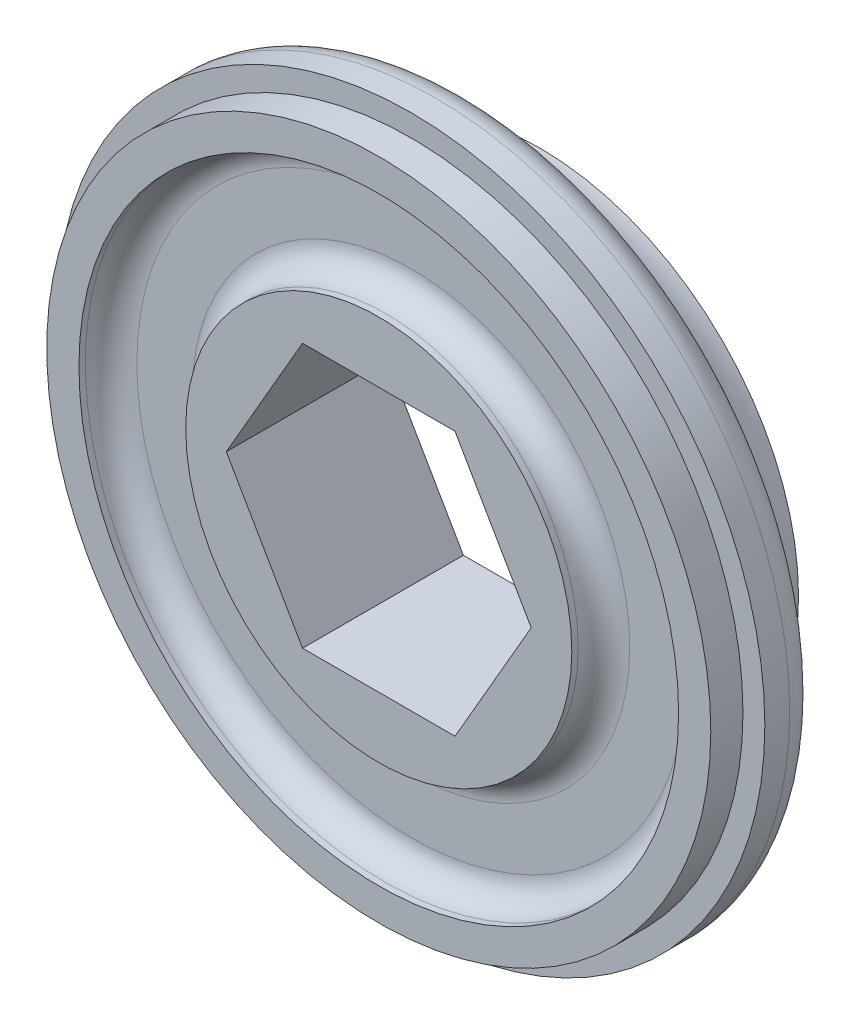
SolidWorks part; units mm, degrees
ref_plane "Front Plane" through (0, 0, 0) normal (0, 0, 1) x (1, 0, 0)
ref_plane "Top Plane" through (0, 0, 0) normal (0, 1, 0) x (1, 0, 0)
ref_plane "Right Plane" through (0, 0, 0) normal (1, 0, 0) x (0, 0, -1)
sketch "Sketch1" plane through (0, 0, 0) normal (0, 0, 1) x (1, 0, 0)
  line L1 (-7.523, 0) -> (-3.7615, -6.5151)
  line L2 (-3.7615, -6.5151) -> (3.7615, -6.5151)
  line L3 (3.7615, -6.5151) -> (7.523, 0)
  line L4 (7.523, 0) -> (3.7615, 6.5151)
  line L5 (3.7615, 6.5151) -> (-3.7615, 6.5151)
  line L6 (-3.7615, 6.5151) -> (-7.523, 0)
  circle A0 centre (0, 0) radius 6.5151 construction
  circle A1 centre (0, 0) radius 17.4625
  dimension "D1" = 34.925
  dimension "D2" = 13.0302
extrude "Hex Axel Cutout & Outside Rim" add sketch "Sketch1" along normal blind 15.875
sketch "Sketch3" plane through (0, 0, 15.875) normal (0, 0, 1) x (1, 0, 0)
  circle A0 centre (0, 0) radius 16.383
  circle A1 centre (0, 0) radius 19.05
  dimension "D1" = 32.766
extrude "Pipe Step" cut sketch "Sketch3" against normal blind 1.5875
ref_plane "Mid Plane" through (0, 0, 7.9375) normal (0, 0, 1) x (1, 0, 0)
mirror "Step Mirror" about plane through (0, 0, 7.9375) normal (0, 0, 1) of "Pipe Step"
ref_axis "Center Axis" through (0, 0, 14.2875) along (0, 0, -1)
sketch "Sketch4" plane through (0, 0, 0) normal (1, 0, 0) x (0, 0, -1)
  line L0 (-1.5875, -17.4625) -> (-1.5875, 17.4625) construction
  line L1 (-1.5875, -17.4625) -> (-1.5875, 17.4625) construction
  line L2 (-14.2875, 17.4625) -> (-14.2875, -17.4625) construction
  line L3 (-14.2875, 17.4625) -> (-14.2875, -17.4625) construction
  line L4 (-1.5875, 17.4625) -> (-14.2875, 17.4625) construction
  line L5 (-4.3815, 16.3317) -> (-4.3815, 17.4625)
  line L6 (-4.3815, 17.4625) -> (-11.4935, 17.4625)
  line L7 (-11.4935, 17.4625) -> (-11.4935, 16.3317)
  arc A0 (-11.4935, 16.3317) -> (-4.3815, 16.3317) centre (-7.9375, 16.3317) ccw
  dimension "D1" = 7.112
  dimension "D2" = 1.1308
revolve "Poly Cord Groove" cut sketch "Sketch4" angle 360 about axis through (0, 0, 14.2875) along (0, 0, -1)
sketch "Sketch5" plane through (0, 0, 0) normal (0, 0, -1) x (-1, 0, 0)
  circle A0 centre (0, 0) radius 9.525
  circle A1 centre (0, 0) radius 14.7955
  circle A2 centre (0, 0) radius 16.383 construction
  dimension "D1" = 1.5875
extrude "Spoke Step" cut sketch "Sketch5" against normal blind 1.5875
mirror "Spoke Step Mirror" about plane through (0, 0, 7.9375) normal (0, 0, 1) of "Spoke Step"
sketch "Sketch6" plane through (0, 0, 14.2875) normal (0, 0, 1) x (1, 0, 0)
  line L0 (9.525, 0) -> (14.7955, 0) construction
  arc A0 (11.2346, -4.6535) -> (11.2346, 4.6535) centre (0, 0) ccw construction
  arc A1 (12.5253, -5.1881) -> (12.5253, 5.1881) centre (0, 0) ccw
  circle A2 centre (0, 0) radius 9.525 construction
  circle A3 centre (0, 0) radius 14.7955 construction
  arc A4 (9.9439, -4.1189) -> (9.9439, 4.1189) centre (0, 0) ccw
  arc A5 (9.9439, -4.1189) -> (12.5253, -5.1881) centre (11.2346, -4.6535) ccw
  arc A6 (12.5253, 5.1881) -> (9.9439, 4.1189) centre (11.2346, 4.6535) ccw
  arc A7 (-4.6535, -11.2346) -> (4.6535, -11.2346) centre (0, 0) ccw construction
  arc A8 (-5.1881, -12.5253) -> (5.1881, -12.5253) centre (0, 0) ccw
  arc A9 (-4.1189, -9.9439) -> (4.1189, -9.9439) centre (0, 0) ccw
  arc A10 (-4.1189, -9.9439) -> (-5.1881, -12.5253) centre (-4.6535, -11.2346) ccw
  arc A11 (5.1881, -12.5253) -> (4.1189, -9.9439) centre (4.6535, -11.2346) ccw
  arc A12 (-11.2346, 4.6535) -> (-11.2346, -4.6535) centre (0, 0) ccw construction
  arc A13 (-12.5253, 5.1881) -> (-12.5253, -5.1881) centre (0, 0) ccw
  arc A14 (-9.9439, 4.1189) -> (-9.9439, -4.1189) centre (0, 0) ccw
  arc A15 (-9.9439, 4.1189) -> (-12.5253, 5.1881) centre (-11.2346, 4.6535) ccw
  arc A16 (-12.5253, -5.1881) -> (-9.9439, -4.1189) centre (-11.2346, -4.6535) ccw
  arc A17 (4.6535, 11.2346) -> (-4.6535, 11.2346) centre (0, 0) ccw construction
  arc A18 (5.1881, 12.5253) -> (-5.1881, 12.5253) centre (0, 0) ccw
  arc A19 (4.1189, 9.9439) -> (-4.1189, 9.9439) centre (0, 0) ccw
  arc A20 (4.1189, 9.9439) -> (5.1881, 12.5253) centre (4.6535, 11.2346) ccw
  arc A21 (-5.1881, 12.5253) -> (-4.1189, 9.9439) centre (-4.6535, 11.2346) ccw
  point P9 (12.1602, 0)
  point P14 (12.1602, 0)
  point P20 (0, -12.1602)
  point P27 (-12.1602, 0)
  point P34 (0, 12.1602)
  point P39 (0, 0)
  dimension "D1" = 4
extrude "Slots" [suppressed] cut sketch "Sketch6" against normal through all
fillet "Fillet1" radius 1.27 4 edges at (-9.525, 0, 14.2875) (-14.7955, 0, 14.2875) (-9.525, 0, 1.5875) (-14.7955, 0, 1.5875)
fillet "Fillet2" radius 1.5875 2 edges at (17.4625, 0, 4.3815) (17.4625, 0, 11.4935)
sketch "Sketch7" plane through (0, 0, 7.9375) normal (0, 0, 1) x (1, 0, 0)
  line L1 (23.9973, 33.2603) -> (-26.4119, 33.2603)
  line L2 (23.9973, 33.2603) -> (23.9973, -40.0267)
  line L3 (23.9973, -40.0267) -> (-26.4119, -40.0267)
  line L4 (-26.4119, 33.2603) -> (-26.4119, -40.0267)
extrude "MidCut" cut sketch "Sketch7" against normal through all
